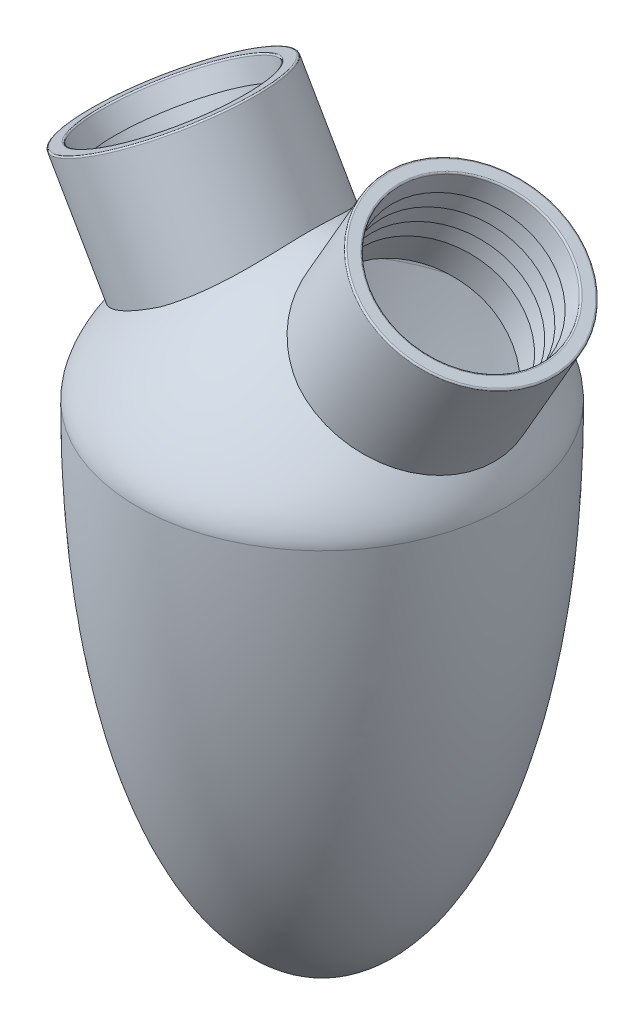
SolidWorks part; units mm, degrees
ref_plane "Front Plane" through (0, 0, 0) normal (0, 0, 1) x (1, 0, 0)
ref_plane "Top Plane" through (0, 0, 0) normal (0, 1, 0) x (1, 0, 0)
ref_plane "Right Plane" through (0, 0, 0) normal (1, 0, 0) x (0, 0, -1)
sketch "Sketch1" plane through (0, 0, 0) normal (0, 0, 1) x (1, 0, 0)
  line L0 (0, 0) -> (35, 0) construction
  line L1 (0, 0) -> (0, -93.4) construction
  line L2 (0, 0) -> (0, 26.2) construction
  line L3 (0, 27.5) -> (0, 26.2)
  line L4 (35, 0) -> (36.3, 0) construction
  line L5 (0, -93.4) -> (0, -94.7)
  line L6 (35, -22.1743) -> (35, 22.1743) construction
  line L7 (36.3, -22.597) -> (36.3, 22.597) construction
  line L8 (49.2989, 26.2) -> (-49.2989, 26.2) construction
  line L9 (49.5531, 27.5) -> (-49.5531, 27.5) construction
  line L10 (-48.0253, -93.4) -> (48.0253, -93.4) construction
  line L11 (-50.8791, -94.7) -> (50.8791, -94.7) construction
  line L12 (36.3, -190.517) -> (36.3, 190.517) construction
  line L13 (35, -187.8676) -> (35, 187.8676) construction
  spline S0 degree 3 poles (35, 0) (35, -62.3333) (16.6667, -93.4) (0, -93.4) knots 0 0 0 0 1 1 1 1
  spline S1 degree 3 poles (36.3, 0) (36.3, -63.3333) (17.3333, -94.7) (0, -94.7) knots 0 0 0 0 1 1 1 1
  spline S2 degree 3 poles (0, 27.5) (17, 27.5) (36.3, 7.6667) (36.3, 0) knots 0 0 0 0 1 1 1 1
  spline S3 degree 3 poles (0, 26.2) (16.6667, 26.2) (35, 7.3333) (35, 0) knots 0 0 0 0 1 1 1 1
  dimension "D7" = 90
  dimension "D8" = 90
  dimension "D9" = 23
  dimension "D10" = 22
  dimension "D11" = 90
  dimension "D12" = 90
  dimension "D13" = 50
  dimension "D14" = 51
  dimension "D15" = 90
  dimension "D16" = 90
  dimension "D17" = 50
  dimension "D18" = 52
  dimension "D19" = 90
  dimension "D20" = 90
  dimension "D21" = 190
  dimension "D22" = 187
  dimension "D1" = 1.3
  dimension "D2" = 93.4
  dimension "D3" = 35
  dimension "D4" = 1.3
  dimension "D5" = 1.3
  dimension "D6" = 26.2
revolve "Revolve1" add sketch "Sketch1" angle 360 about L1
ref_plane "Plane1" through (0, 30, 0) normal (0, 1, 0) x (1, 0, 0)
sketch "Sketch2" plane through (0, 30, 0) normal (0, 1, 0) x (1, 0, 0)
  line L0 (0, 40.4379) -> (0, -39.6549)
ref_plane "Plane2" through (-12.9904, 22.5, 0) normal (-0.5, 0.866, 0) x (0, 0, 1)
sketch "Sketch4" plane through (-12.9904, 22.5, 0) normal (-0.5, 0.866, 0) x (0, 0, 1)
  circle A0 centre (0, -7.3235) radius 18.775
  ellipse E0 centre (0, 0) end of major axis (36.3, 0) minor radius 31.4367 construction
  dimension "D1" = 37.55
extrude "Boss-Extrude1" add sketch "Sketch4" along normal blind 20 and the other way blind 3.5 contours A0
ref_plane "Plane3" through (12.9904, 22.5, 0) normal (0.5, 0.866, 0) x (0, 0, 1)
sketch "Sketch5" plane through (12.9904, 22.5, 0) normal (0.5, 0.866, 0) x (0, 0, 1)
  circle A0 centre (0, 7.3124) radius 18.775
  ellipse E0 centre (0, 0) end of major axis (-36.3, 0) minor radius 31.4367 construction
  dimension "D1" = 37.55
extrude "Boss-Extrude2" add sketch "Sketch5" along normal blind 20 and the other way blind 3.5 contours A0
sketch "Sketch6" plane through (-22.9904, 39.8205, 0) normal (-0.5, 0.866, 0) x (0.866, 0.5, 0)
  circle A0 centre (-7.3235, 0) radius 16.125
  dimension "D1" = 32.25
extrude "Cut-Extrude1" cut sketch "Sketch6" against normal blind 24.3
sketch "Sketch7" plane through (22.9904, 39.8205, 0) normal (0.5, 0.866, 0) x (0.866, -0.5, 0)
  circle A1 centre (7.3124, 0) radius 16.125
  dimension "D1" = 32.25
extrude "Cut-Extrude2" cut sketch "Sketch7" against normal blind 24.3 contours A1
ref_plane "Plane4" through (0, -100, 0) normal (0, -1, 0) x (-1, 0, 0)
sketch "Sketch8" plane through (0, -100, 0) normal (0, -1, 0) x (-1, 0, 0)
  line L0 (0, 44.7561) -> (0, -42.6156)
fillet "Fillet1" radius 0.3 4 edges at (13.0635, 45.5518, 0) (15.3584, 44.2268, 0) (-45.5923, 26.7713, 0) (-43.2974, 28.0963, 0)
ref_plane "Plane5" through (0, 0, 36.3) normal (0, 0, 1) x (1, 0, 0)
ref_plane "Plane6" through (0, -100, 0) normal (0, -1, 0) x (-1, 0, 0)
sketch "Sketch11" plane through (12.9904, 22.5, 0) normal (0.5, 0.866, 0) x (0, 0, 1)
  circle A0 centre (0, 7.3124) radius 3
extrude "Cut-Extrude3" [suppressed] cut sketch "Sketch11" against normal through all
sketch "Sketch12" plane through (-12.9904, 22.5, 0) normal (-0.5, 0.866, 0) x (0, 0, 1)
  circle A0 centre (0, -7.3235) radius 3
extrude "Cut-Extrude4" [suppressed] cut sketch "Sketch12" against normal through all
sketch "Sketch19" plane through (-12.9904, 22.5, 0) normal (-0.5, 0.866, 0) x (0, 0, 1)
  line L0 (0, 8.8015) -> (0, -23.7485)
  circle A0 centre (0, -7.3235) radius 16.125 construction
  circle A1 centre (0, -7.3235) radius 16.425 construction
ref_plane "Plane9" through (0, 0, 0) normal (0, 0, -1) x (-0.866, -0.5, 0)
sketch "Sketch20" plane through (0, 0, 0) normal (0, 0, -1) x (-0.866, -0.5, 0)
  line L0 (-8.8015, 45.6808) -> (-8.8015, 41.6808)
  line L1 (-8.8015, 45.6808) -> (-8.8015, 22.4808) construction
  line L2 (-8.8015, 41.6808) -> (-8.2015, 41.6808)
  line L3 (-8.2015, 41.6808) -> (-8.8015, 45.6808)
  dimension "D1" = 4
  dimension "D2" = 0.6
sketch "Sketch21" plane through (0, 0, 0) normal (0, 0, -1) x (-0.866, -0.5, 0)
  line L0 (7.3235, 45.6808) -> (7.3235, 22.4808)
  line L1 (26.0985, 45.6808) -> (-11.4515, 45.6808) construction
  line L2 (-7.8085, 22.4808) -> (6.2753, 22.4808) construction
sketch "Sketch22" plane through (12.9904, 22.5, 0) normal (0.5, 0.866, 0) x (0, 0, 1)
  line L0 (0, 23.4374) -> (0, -8.8126)
  circle A0 centre (0, 7.3124) radius 16.125 construction
ref_plane "Plane10" through (0, 0, 0) normal (0, 0, -1) x (-0.866, 0.5, 0)
sketch "Sketch23" plane through (0, 0, 0) normal (0, 0, -1) x (-0.866, 0.5, 0)
  line L0 (-23.4374, 45.6808) -> (-23.4374, 41.6808)
  line L1 (-23.4374, 45.6808) -> (-23.4374, 22.4199) construction
  line L2 (-23.4374, 41.6808) -> (-22.8374, 41.6808)
  line L3 (-22.8374, 41.6808) -> (-23.4374, 45.6808)
  dimension "D1" = 4
  dimension "D2" = 0.6
sketch "Sketch24" plane through (0, 0, 0) normal (0, 0, -1) x (-0.866, 0.5, 0)
  line L0 (-7.3124, 45.6808) -> (-7.3124, 25.9808)
  line L1 (11.4626, 45.6808) -> (-26.0874, 45.6808) construction
  line L2 (-23.4374, 25.9808) -> (8.8126, 25.9808) construction
revolve "Revolve2" add sketch "Sketch23" angle 360 about L0
pattern_linear "LPattern1" count 4 spacing 4 along (-0.5, -0.866, 0) of "Revolve2"
revolve "Revolve3" add sketch "Sketch20" angle 360 about L0
pattern_linear "LPattern2" count 4 spacing 4 along (0.5, -0.866, 0) of "Revolve3"
